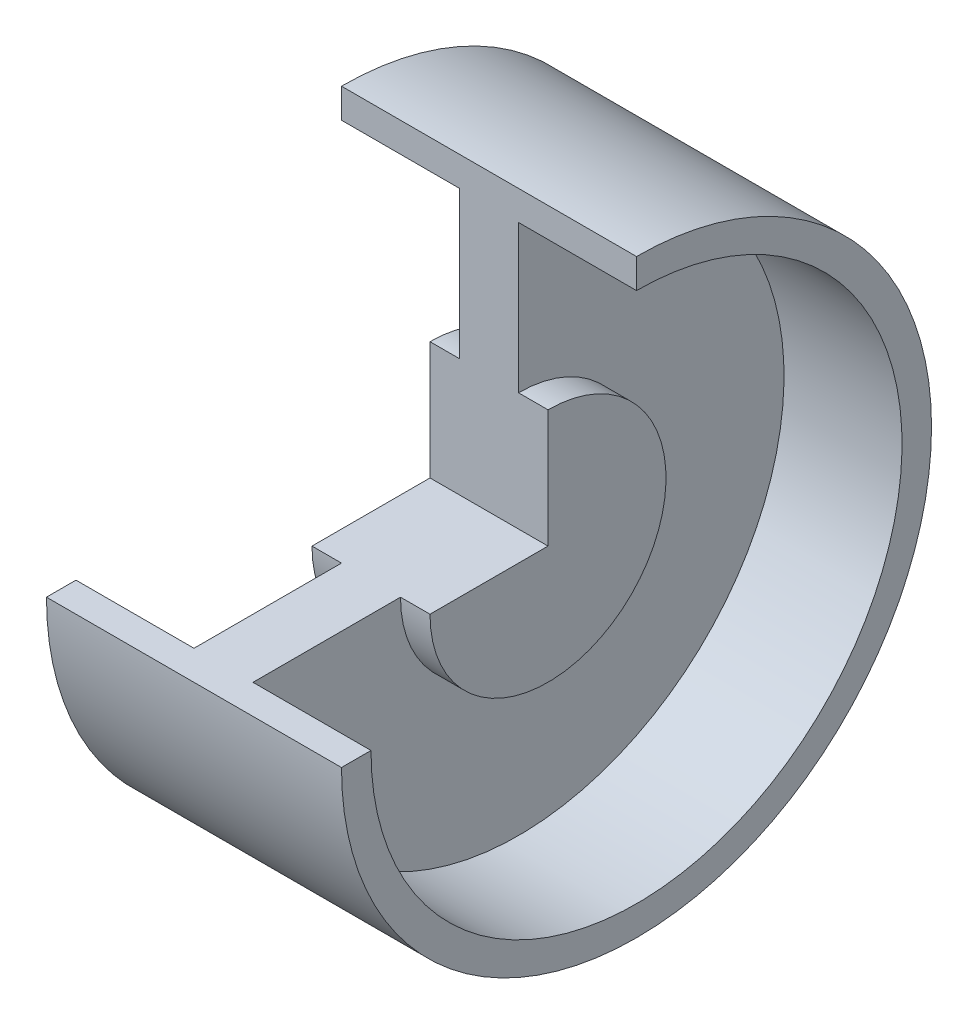
SolidWorks part; units mm, degrees
ref_plane "Front Plane" through (0, 0, 0) normal (0, 0, 1) x (1, 0, 0)
ref_plane "Top Plane" through (0, 0, 0) normal (0, 1, 0) x (1, 0, 0)
ref_plane "Right Plane" through (0, 0, 0) normal (1, 0, 0) x (0, 0, -1)
sketch "Sketch1" plane through (0, 0, 0) normal (0, 0, 1) x (1, 0, 0)
  line L0 (-10, 0) -> (10, 0)
  line L1 (10, 0) -> (10, 20)
  line L2 (10, 20) -> (5, 20)
  line L3 (5, 20) -> (5, 45)
  line L4 (5, 45) -> (25, 45)
  line L5 (25, 45) -> (25, 50)
  line L6 (25, 50) -> (-25, 50)
  line L7 (0, 50) -> (0, 0) construction
  line L8 (-25, 45) -> (-25, 50)
  line L9 (-5, 45) -> (-25, 45)
  line L10 (-5, 20) -> (-5, 45)
  line L11 (-10, 20) -> (-5, 20)
  line L12 (-10, 0) -> (-10, 20)
  dimension "D1" = 20
  dimension "D2" = 25
  dimension "D3" = 5
  dimension "D4" = 20
  dimension "D5" = 10
  dimension "D6" = 50
revolve "Revolve2" add sketch "Sketch1" angle 270 about L0
